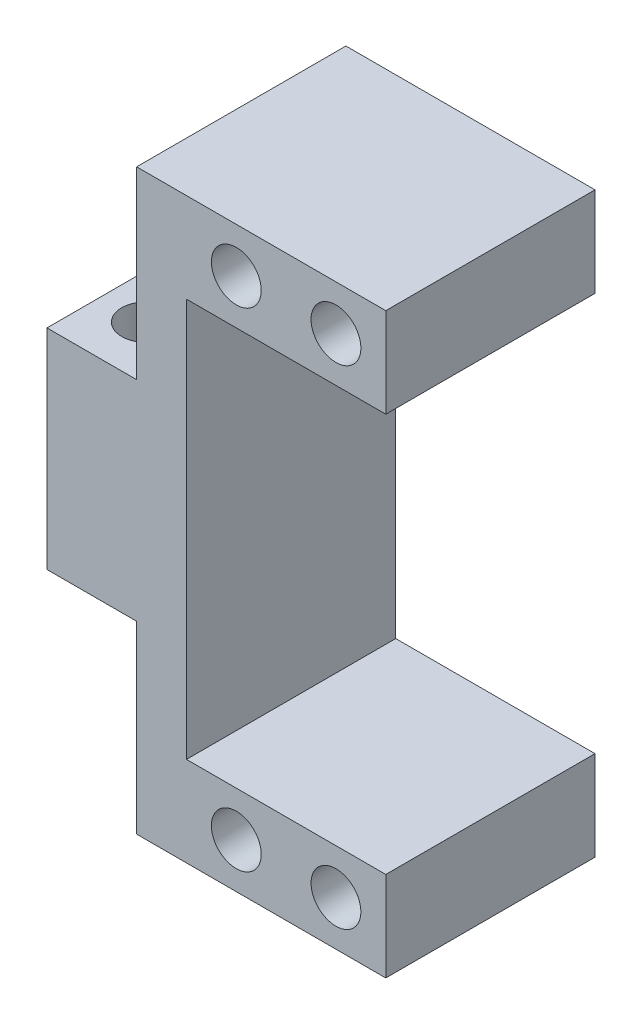
SolidWorks part; units mm, degrees
ref_plane "Face" through (0, 0, 0) normal (0, 0, 1) x (1, 0, 0)
ref_plane "Dessus" through (0, 0, 0) normal (0, 1, 0) x (1, 0, 0)
ref_plane "Droite" through (0, 0, 0) normal (1, 0, 0) x (0, 0, -1)
sketch "Esquisse1" plane through (0, 0, 0) normal (0, 0, 1) x (1, 0, 0)
  line L0 (0, -10.5) -> (0, 10.5)
  line L1 (0, 10.5) -> (9, 10.5)
  line L2 (9, 10.5) -> (9, 29)
  line L3 (9, 29) -> (34, 29)
  line L4 (34, 29) -> (34, 20)
  line L5 (34, 20) -> (14, 20)
  line L6 (14, 20) -> (14, -20)
  line L7 (-113.1151, 0) -> (121.7235, 0) construction
  line L8 (55, 0) -> (-55, 0) construction
  line L9 (34, -20) -> (14, -20)
  line L10 (34, -29) -> (34, -20)
  line L11 (9, -29) -> (34, -29)
  line L12 (9, -10.5) -> (9, -29)
  line L13 (0, -10.5) -> (9, -10.5)
  point P14 (14, 0)
  point P19 (0, 0)
  dimension "D1" = 21
  dimension "D2" = 40
  dimension "D3" = 9
  dimension "D4" = 5
  dimension "D5" = 9
  dimension "D6" = 20
extrude "Extrusion1" add sketch "Esquisse1" along normal blind 21
sketch "Esquisse2" plane through (0, 0, 21) normal (0, 0, 1) x (1, 0, 0)
  line L0 (-17.7222, 0) -> (59.0716, 0) construction
  line L1 (14, 20) -> (34, 20) construction
  line L2 (34, -20) -> (14, -20) construction
  line L3 (24, 21.5329) -> (24, -18.5522) construction
  line L4 (34, 20) -> (34, 29) construction
  line L5 (14, -20) -> (14, 20) construction
  circle A0 centre (29, 24.5) radius 2.5
  circle A1 centre (19, 24.5) radius 2.5
  circle A2 centre (19, -24.5) radius 2.5
  circle A3 centre (29, -24.5) radius 2.5
  dimension "D3" = 5
  dimension "D1" = 4.5
  dimension "D2" = 10
extrude "Enlèv. mat.-Extru.1" cut sketch "Esquisse2" against normal through all
sketch "Esquisse3" plane through (0, 10.5, 0) normal (0, 1, 0) x (1, 0, 0)
  line L0 (-3.1364, -10.5) -> (19.9205, -10.5) construction
  line L1 (9, 0) -> (0, 0) construction
  line L2 (9, -21) -> (0, -21) construction
  line L3 (0, -21) -> (0, 0) construction
  circle A0 centre (4.5, -5.5) radius 2.5
  circle A1 centre (4.5, -15.5) radius 2.5
  dimension "D3" = 5
  dimension "D1" = 4.5
  dimension "D2" = 10
extrude "Enlèv. mat.-Extru.2" cut sketch "Esquisse3" against normal through all
